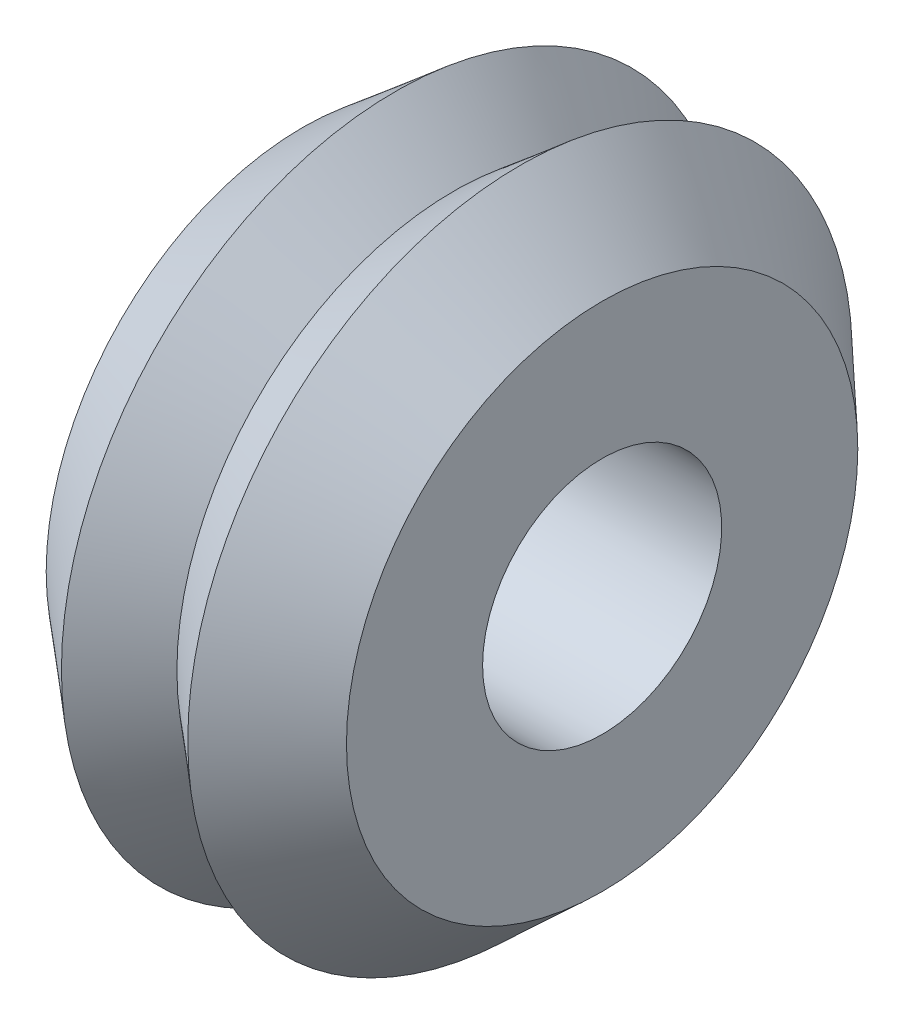
SolidWorks part; units mm, degrees
ref_plane "Front Plane" through (0, 0, 0) normal (0, 0, 1) x (1, 0, 0)
ref_plane "Top Plane" through (0, 0, 0) normal (0, 1, 0) x (1, 0, 0)
ref_plane "Right Plane" through (0, 0, 0) normal (1, 0, 0) x (0, 0, -1)
sketch "Sketch1" plane through (0, 0, 0) normal (0, 0, 1) x (1, 0, 0)
  line L0 (-55.0196, 84.2778) -> (55.0196, 84.2778)
  line L2 (-55.0196, -22.3724) -> (-55.0196, 22.3724)
  line L3 (-55.0196, 22.3724) -> (55.0196, 22.3724)
  line L4 (55.0196, -22.3724) -> (55.0196, 22.3724)
  line L7 (-55.0196, -22.3724) -> (-25.2202, -47.2915)
  line L8 (-25.2202, -47.2915) -> (0, -22.3724)
  line L9 (0, -22.3724) -> (29.0141, -46.6349)
  line L10 (29.0141, -46.6349) -> (55.0196, -22.3724)
  point P0 (0, 0)
revolve "Revolve-Thin2" add sketch "Sketch1" angle 360 about L0
sketch "Sketch2" plane through (-65.0196, 0, 0) normal (-1, 0, 0) x (0, 0, 1)
  line L0 (-51.9054, 84.2778) -> (-76.7121, 84.2778)
  line L1 (-76.7121, 84.2778) -> (-74.3414, 89.4332)
  line L2 (-40.8754, 116.4983) -> (-40.655, 116.5477)
  line L3 (-40.655, 116.5477) -> (-45.4279, 109.3871)
  line L4 (-45.4279, 109.3871) -> (-49.6169, 99.5203)
  line L5 (-49.6169, 99.5203) -> (-51.6487, 89.4332)
  line L6 (-51.6487, 89.4332) -> (-51.9054, 84.2778)
  line L7 (-25.9527, 129.2292) -> (-38.3561, 150.7125)
  line L8 (-38.3561, 150.7125) -> (-32.706, 151.2371)
  line L9 (7.4661, 135.7872) -> (7.6191, 135.621)
  line L10 (7.6191, 135.621) -> (-0.9686, 136.1742)
  line L11 (-0.9686, 136.1742) -> (-11.6081, 134.8686)
  line L12 (-11.6081, 134.8686) -> (-21.3596, 131.5846)
  line L13 (-21.3596, 131.5846) -> (-25.9527, 129.2292)
  line L14 (25.9527, 129.2292) -> (38.3561, 150.7125)
  line L15 (38.3561, 150.7125) -> (41.6354, 146.0817)
  line L16 (48.3415, 103.5667) -> (48.274, 103.3511)
  line L17 (48.274, 103.3511) -> (44.4593, 111.0648)
  line L18 (44.4593, 111.0648) -> (38.0088, 119.6261)
  line L19 (38.0088, 119.6261) -> (30.2891, 126.4292)
  line L20 (30.2891, 126.4292) -> (25.9527, 129.2292)
  line L21 (51.9054, 84.2778) -> (76.7121, 84.2778)
  line L22 (76.7121, 84.2778) -> (74.3414, 79.1224)
  line L23 (40.8754, 52.0573) -> (40.655, 52.0079)
  line L24 (40.655, 52.0079) -> (45.4279, 59.1685)
  line L25 (45.4279, 59.1685) -> (49.6169, 69.0353)
  line L26 (49.6169, 69.0353) -> (51.6487, 79.1224)
  line L27 (51.6487, 79.1224) -> (51.9054, 84.2778)
  line L28 (25.9527, 39.3264) -> (38.3561, 17.8432)
  line L29 (38.3561, 17.8432) -> (32.706, 17.3185)
  line L30 (-7.4661, 32.7684) -> (-7.6191, 32.9346)
  line L31 (-7.6191, 32.9346) -> (0.9686, 32.3815)
  line L32 (0.9686, 32.3815) -> (11.6081, 33.6871)
  line L33 (11.6081, 33.6871) -> (21.3596, 36.971)
  line L34 (21.3596, 36.971) -> (25.9527, 39.3264)
  line L35 (-25.9527, 39.3264) -> (-38.3561, 17.8432)
  line L36 (-38.3561, 17.8432) -> (-41.6354, 22.4739)
  line L37 (-48.3415, 64.989) -> (-48.274, 65.2045)
  line L38 (-48.274, 65.2045) -> (-44.4593, 57.4908)
  line L39 (-44.4593, 57.4908) -> (-38.0088, 48.9295)
  line L40 (-38.0088, 48.9295) -> (-30.2891, 42.1264)
  line L41 (-30.2891, 42.1264) -> (-25.9527, 39.3264)
  circle A0 centre (0, 84.2778) radius 51.9054 construction
  arc A1 (-74.3414, 89.4332) -> (-40.8754, 116.4983) centre (-30.2771, 69.1705) cw
  arc A2 (-32.706, 151.2371) -> (7.4661, 135.7872) centre (-28.2219, 102.9448) cw
  arc A3 (41.6354, 146.0817) -> (48.3415, 103.5667) centre (2.0552, 118.0522) cw
  arc A4 (74.3414, 79.1224) -> (40.8754, 52.0573) centre (30.2771, 99.3851) cw
  arc A5 (32.706, 17.3185) -> (-7.4661, 32.7684) centre (28.2219, 65.6108) cw
  arc A6 (-41.6354, 22.4739) -> (-48.3415, 64.989) centre (-2.0552, 50.5035) cw
  point P60 (0, 84.2778)
  dimension "D1" = 48.5
  dimension "D2" = 6
extrude "Boss-Extrude3" add sketch "Sketch2" along normal blind 20
